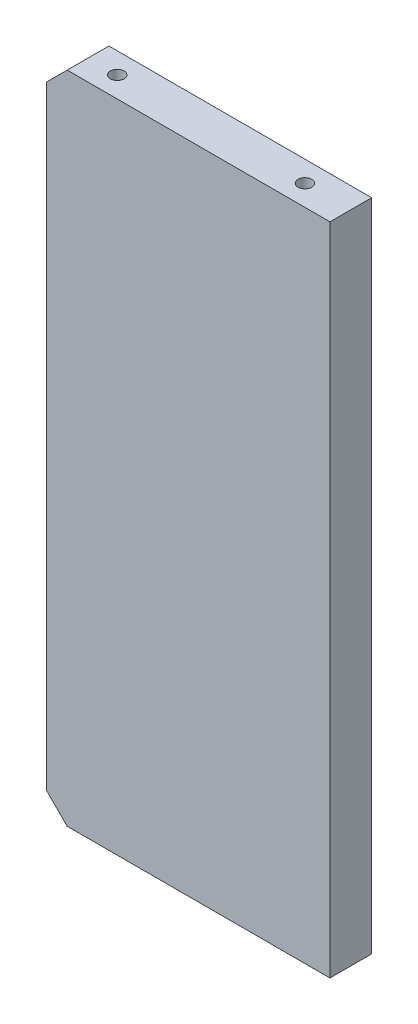
SolidWorks part; units mm, degrees
ref_plane "Front" through (0, 0, 0) normal (0, 0, 1) x (1, 0, 0)
ref_plane "Top" through (0, 0, 0) normal (0, 1, 0) x (1, 0, 0)
ref_plane "Right" through (0, 0, 0) normal (1, 0, 0) x (0, 0, -1)
sketch "Sketch1" plane through (0, 0, 0) normal (0, 0, 1) x (1, 0, 0)
  line L0 (-7.1434, 0) -> (72.4482, 0) construction
  line L2 (68, -78.5) -> (0, -78.5)
  line L3 (68, -78.5) -> (68, 78.5)
  line L4 (68, 78.5) -> (0, 78.5)
  line L5 (0, -78.5) -> (0, 78.5)
  dimension "D1" = 68
  dimension "D2" = 157
extrude "Boss-Extrude1" add sketch "Sketch1" against normal blind 10
hole_wizard "M5x0.8 Tapped Hole1" positions "Sketch3" profile "Sketch2" tap size "M5x0.8" standard "JIS"
sketch "Sketch3" plane through (0, 0, 0) normal (-1, 0, 0) x (0, 0, 1)
  line L0 (10.7492, 0) -> (-30.2552, 0) construction
  point P0 (-5, 58.5)
  point P1 (-5, 0)
  point P3 (-5, -58.5)
  dimension "D1" = 117
  dimension "D3" = 5
sketch "Sketch2" plane through (0, 58.5, -5) normal (0, 1, 0) x (0, 0, 1)
  line L0 (0, 0) -> (0, 13.6618)
  line L1 (0, 13.6618) -> (2.1, 12.4)
  line L2 (2.1, 12.4) -> (2.1, 0)
  line L5 (2.1, 0) -> (0, 0)
  line L10 (0, 13.6618) -> (-2.1, 12.4) construction
  line L11 (0, -6.35) -> (0, 107.95) construction
  dimension "Tap Drill Dia." = 4.2
  dimension "Tap Drill Depth" = 12.4
  dimension "Drill Angle" = 118
cosmetic thread "Hole Thread1" parameters "D1"=10, "D2"=5
cosmetic thread "Hole Thread2" parameters "D1"=10, "D2"=5
cosmetic thread "Hole Thread3" parameters "D1"=10, "D2"=5
hole_wizard "M4x0.7 Tapped Hole1" positions "Sketch5" profile "Sketch4" tap size "M4x0.7" standard "JIS"
sketch "Sketch5" plane through (0, 78.5, 0) normal (0, 1, 0) x (-1, 0, 0)
  point P0 (-12, -5)
  point P2 (-57, -5)
  dimension "D1" = 5
  dimension "D2" = 45
  dimension "D3" = 12
sketch "Sketch4" plane through (12, 78.5, -5) normal (1, 0, 0) x (0, 0, 1)
  line L0 (0, 0) -> (0, 17.0914)
  line L1 (0, 17.0914) -> (1.65, 16.1)
  line L2 (1.65, 16.1) -> (1.65, 0)
  line L5 (1.65, 0) -> (0, 0)
  line L10 (0, 17.0914) -> (-1.65, 16.1) construction
  line L11 (0, -6.35) -> (0, 107.95) construction
  dimension "Tap Drill Dia." = 3.3
  dimension "Tap Drill Depth" = 16.1
  dimension "Drill Angle" = 118
cosmetic thread "Hole Thread4" parameters "D1"=14, "D2"=4
cosmetic thread "Hole Thread5" parameters "D1"=14, "D2"=4
mirror "Mirror1" about plane through (0, 0, 0) normal (0, 1, 0) of "M4x0.7 Tapped Hole1"
chamfer "Chamfer1" distance 5 angle 45 2 edges at (0, -78.5, -5) (0, 78.5, -5)
